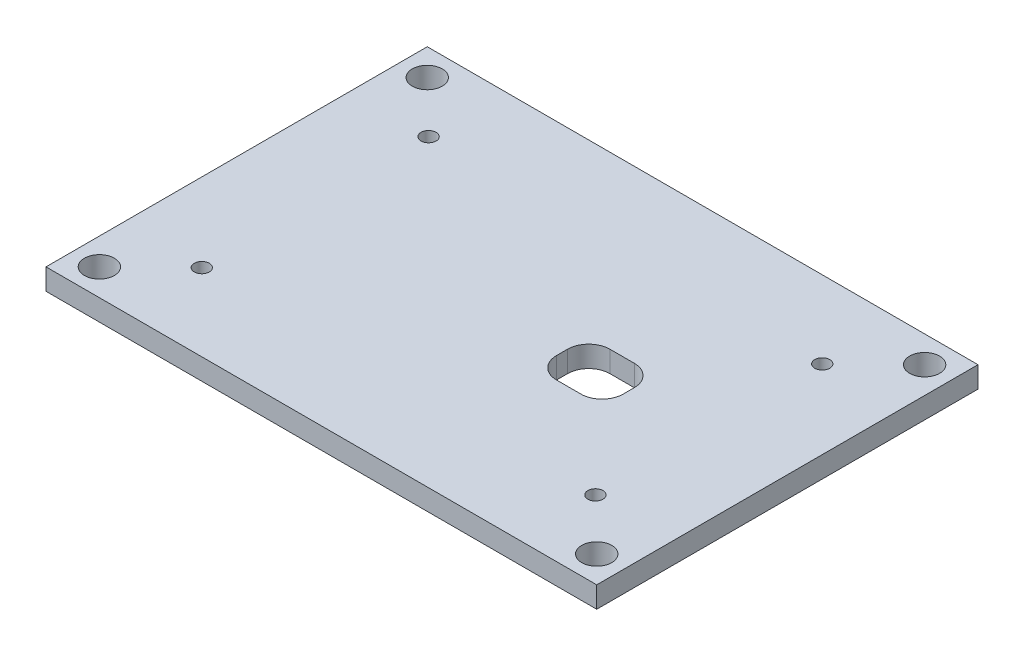
SolidWorks part; units mm, degrees
material "Delrin 2700 NC010, Low Viscosity Acetal Copolymer (SS)"
ref_plane "Front Plane" through (0, 0, 0) normal (0, 0, 1) x (1, 0, 0)
ref_plane "Top Plane" through (0, 0, 0) normal (0, 1, 0) x (1, 0, 0)
ref_plane "Right Plane" through (0, 0, 0) normal (1, 0, 0) x (0, 0, -1)
sketch "Sketch1" plane through (0, 0, 0) normal (0, 1, 0) x (1, 0, 0)
  line L1 (41.275, -28.575) -> (-41.275, -28.575)
  line L2 (41.275, -28.575) -> (41.275, 28.575)
  line L3 (41.275, 28.575) -> (-41.275, 28.575)
  line L4 (-41.275, -28.575) -> (-41.275, 28.575)
  line L5 (41.275, -28.575) -> (-41.275, 28.575) construction
  line L6 (41.275, 28.575) -> (-41.275, -28.575) construction
  point P0 (0, 0)
  dimension "D1" = 82.55
  dimension "D2" = 57.15
extrude "Boss-Extrude1" add sketch "Sketch1" along normal blind 3.175
sketch "Sketch2" plane through (0, 0, 0) normal (0, -1, 0) x (1, 0, 0)
  line L0 (8.5, 1.825) -> (8.5, 0.175)
  line L5 (11.675, -3) -> (15.325, -3)
  line L6 (18.5, 0.175) -> (18.5, 1.825)
  line L7 (15.325, 5) -> (11.675, 5)
  line L8 (9.5, 4) -> (9.5, -2)
  line L9 (9.5, -2) -> (17.5, -2)
  line L10 (17.5, -2) -> (17.5, 4)
  line L11 (17.5, 4) -> (9.5, 4)
  line L12 (9.5, 4) -> (9.5, -2) construction
  line L13 (9.5, -2) -> (17.5, -2) construction
  line L14 (17.5, -2) -> (17.5, 4) construction
  line L15 (17.5, 4) -> (9.5, 4) construction
  line L16 (8.5, 5) -> (8.5, -3) construction
  line L17 (18.5, 5) -> (8.5, 5) construction
  line L18 (8.5, -3) -> (18.5, -3) construction
  line L19 (18.5, -3) -> (18.5, 5) construction
  arc A0 (8.5, 1.825) -> (11.675, 5) centre (11.675, 1.825) cw
  arc A1 (8.5, 0.175) -> (11.675, -3) centre (11.675, 0.175) ccw
  arc A2 (15.325, -3) -> (18.5, 0.175) centre (15.325, 0.175) ccw
  arc A3 (18.5, 1.825) -> (15.325, 5) centre (15.325, 1.825) ccw
  point P11 (8.5, 5)
  dimension "D3" = 3.175
  dimension "D2" = 10
  dimension "D1" = 0
extrude "Cut-Extrude5" cut sketch "Sketch2" against normal blind 10
hole_wizard "#8 Clearance Hole1" positions "Sketch3" profile "Sketch5" hole size "#8" standard "ANSI Inch" end condition through all
sketch "Sketch3" plane through (0, 0, 0) normal (0, -1, 0) x (-1, 0, 0)
  line L1 (37.275, -24.575) -> (-37.275, -24.575)
  line L2 (37.275, -24.575) -> (37.275, 24.575)
  line L3 (37.275, 24.575) -> (-37.275, 24.575)
  line L4 (-37.275, -24.575) -> (-37.275, 24.575)
  line L5 (37.275, -24.575) -> (-37.275, 24.575) construction
  line L6 (37.275, 24.575) -> (-37.275, -24.575) construction
  line L7 (-41.275, 28.575) -> (41.275, 28.575) construction
  line L8 (-41.275, -28.575) -> (-41.275, 28.575) construction
  point P0 (-37.275, 24.575)
  point P2 (37.275, 24.575)
  point P4 (37.275, -24.575)
  point P6 (-37.275, -24.575)
  dimension "D1" = 4
  dimension "D2" = 4
sketch "Sketch5" plane through (37.275, 0, -24.575) normal (1, 0, 0) x (0, 0, -1)
  line L0 (0, 0) -> (0, 3.175)
  line L1 (0, 3.175) -> (2.2479, 3.175)
  line L2 (2.2479, 3.175) -> (2.2479, 0)
  line L5 (2.2479, 0) -> (0, 0)
  line L11 (0, -6.35) -> (0, 107.95) construction
  dimension "Thru Hole Dia." = 4.4958
  dimension "Thru Hole Depth" = 3.175
hole_wizard "#4-40 Tapped Hole1" positions "Sketch6" profile "Sketch8" tap size "#4-40" standard "ANSI Inch" end condition through all
sketch "Sketch6" plane through (0, 3.175, 0) normal (0, 1, 0) x (1, 0, 0)
  point P0 (-29.5, -17)
  point P2 (-29.5, 17)
  point P4 (29.5, 17)
  point P6 (29.5, -17)
sketch "Sketch8" plane through (-29.5, 3.175, 17) normal (1, 0, 0) x (0, 0, 1)
  line L0 (0, 0) -> (0, 3.175)
  line L1 (0, 3.175) -> (1.1303, 3.175)
  line L2 (1.1303, 3.175) -> (1.1303, 0)
  line L5 (1.1303, 0) -> (0, 0)
  line L11 (0, -6.35) -> (0, 107.95) construction
  dimension "Thru Tap Drill Dia." = 2.2606
  dimension "Thru Tap Drill Depth" = 3.175
cosmetic thread "Hole Thread1" parameters "D2"=2.8448
cosmetic thread "Hole Thread2" parameters "D2"=2.8448
cosmetic thread "Hole Thread3" parameters "D2"=2.8448
cosmetic thread "Hole Thread4" parameters "D2"=2.8448
